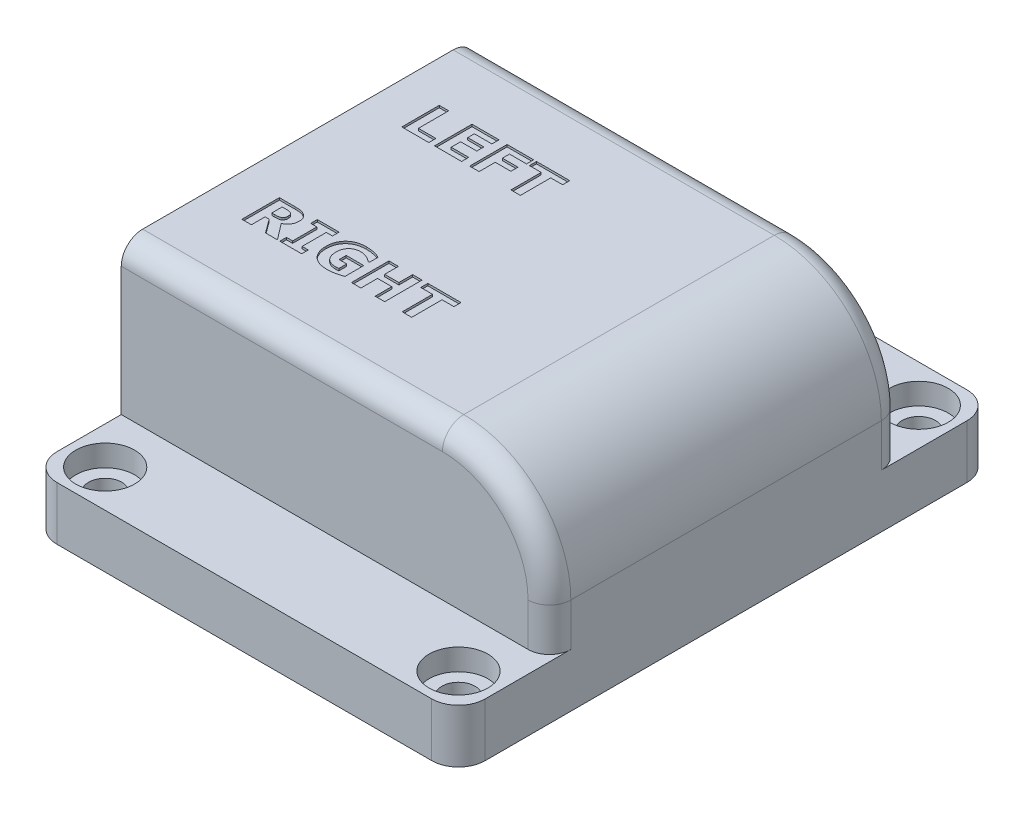
SolidWorks part; units mm, degrees
ref_plane "Front Plane" through (0, 0, 0) normal (0, 0, 1) x (1, 0, 0)
ref_plane "Top Plane" through (0, 0, 0) normal (0, 1, 0) x (1, 0, 0)
ref_plane "Right Plane" through (0, 0, 0) normal (1, 0, 0) x (0, 0, -1)
sketch "Sketch1" plane through (0, 0, 0) normal (0, 1, 0) x (1, 0, 0)
  line L1 (-20, -25) -> (20, -25)
  line L2 (-20, -25) -> (-20, 25)
  line L3 (-20, 25) -> (20, 25)
  line L4 (20, -25) -> (20, 25)
  line L5 (-20, -25) -> (20, 25) construction
  line L6 (-20, 25) -> (20, -25) construction
  point P0 (0, 0)
  dimension "D1" = 50
  dimension "D2" = 40
extrude "Boss-Extrude1" add sketch "Sketch1" along normal blind 5
sketch "Sketch2" plane through (0, 5, 0) normal (0, 1, 0) x (1, 0, 0)
  line L0 (-20, 25) -> (-20, -25) construction
  line L1 (20, -16.5) -> (-20, -16.5)
  line L2 (20, -16.5) -> (20, 16.5)
  line L3 (20, 16.5) -> (-20, 16.5)
  line L4 (-20, -16.5) -> (-20, 16.5)
  line L5 (20, -16.5) -> (-20, 16.5) construction
  line L6 (20, 16.5) -> (-20, -16.5) construction
  point P0 (0, 0)
  dimension "D1" = 33
extrude "Boss-Extrude2" add sketch "Sketch2" along normal blind 14
sketch "Sketch5" plane through (-20, 0, 0) normal (-1, 0, 0) x (0, 0, 1)
  line L0 (0, -1000) -> (0, 49000) construction
  line L1 (-1020.9912, 5) -> (48979.0088, 5) construction
  line L3 (-2, -995) -> (-2, 49005) construction
  line L4 (2, -995) -> (2, 49005) construction
  line L5 (-25, 0) -> (25, 0) construction
  line L6 (-1007.3392, 17.35) -> (48992.6608, 17.35) construction
  line L7 (-14.8, -987.4852) -> (-14.8, 49012.5148) construction
  line L8 (14.8, -989.6407) -> (14.8, 49010.3593) construction
  line L9 (-13.2, -993.3873) -> (-13.2, 49006.6127) construction
  line L10 (-3.6, -993.5926) -> (-3.6, 49006.4074) construction
  line L11 (3.6, -993.3873) -> (3.6, 49006.6127) construction
  line L12 (13.2, -993.6953) -> (13.2, 49006.3047) construction
  line L13 (-1007.9651, 7.5) -> (48992.0349, 7.5) construction
  line L14 (-1008.4622, 7) -> (48991.5378, 7) construction
  line L15 (-2, 5) -> (-3.6, 7)
  line L17 (-13.2, 7) -> (-13.2, 7.5)
  line L18 (-3.6, 7) -> (-3.6, 7.5)
  line L19 (-13.2, 7.5) -> (-14.8, 7.5)
  line L20 (-3.6, 7.5) -> (-2, 7.5)
  line L21 (-14.8, 7.5) -> (-14.8, 17.35)
  line L22 (-14.8, 17.35) -> (-2, 17.35)
  line L23 (-2, 7.5) -> (-2, 17.35)
  line L24 (2, 5) -> (14.8, 5)
  line L25 (2, 5) -> (3.6, 7)
  line L26 (14.8, 5) -> (13.2, 7)
  line L27 (3.6, 7) -> (3.6, 7.5)
  line L28 (13.2, 7) -> (13.2, 7.5)
  line L29 (3.6, 7.5) -> (2, 7.5)
  line L30 (13.2, 7.5) -> (14.8, 7.5)
  line L31 (14.8, 7.5) -> (14.8, 17.35)
  line L32 (2, 7.5) -> (2, 17.35)
  line L33 (2, 17.35) -> (14.8, 17.35)
  line L34 (-2, 5) -> (-13.5, 5)
  line L35 (-13.5, 5) -> (-13.2, 7)
  dimension "D1" = 5
  dimension "D2" = 2
  dimension "D3" = 2
  dimension "D4" = 12.35
  dimension "D5" = 12.8
  dimension "D6" = 12.8
  dimension "D7" = 1.6
  dimension "D8" = 1.6
  dimension "D9" = 1.6
  dimension "D10" = 1.6
  dimension "D11" = 2.5
  dimension "D12" = 2
  dimension "D13" = 3
extrude "Cut-Extrude2" cut sketch "Sketch5" against normal blind 23 contours L35 L34 L15 L18 L20 L23 L22 L21 L19 L17 | L33 L32 L29 L27 L25 L24 L26 L28 L30 L31
sketch "Sketch6" plane through (0, 0, 0) normal (0, -1, 0) x (1, 0, 0)
  line L5 (-1000, 0) -> (49000, 0) construction
  line L6 (-20, -25) -> (-20, 25) construction
  line L7 (3, -15) -> (17, -15)
  line L8 (3, -15) -> (3, 15)
  line L9 (3, 15) -> (17, 15)
  line L10 (17, -15) -> (17, 15)
  line L11 (3, -15) -> (17, 15) construction
  line L12 (3, 15) -> (17, -15) construction
  point P1 (10, 0)
  dimension "D1" = 23
  dimension "D2" = 14
  dimension "D3" = 30
extrude "Cut-Extrude3" cut sketch "Sketch6" against normal blind 17.25
fillet "Fillet1" radius 10 2 edges at (17, 17.25, 0) (20, 19, 0)
sketch "Sketch7" plane through (0, 5, 0) normal (0, 1, 0) x (1, 0, 0)
  line L0 (-17, -989.9572) -> (-17, 49010.0428) construction
  line L1 (-20, 25) -> (-20, 16.5) construction
  line L2 (-1020, 7.75) -> (48980, 7.75) construction
  line L3 (-20, 2) -> (-20, 13.5) construction
  line L4 (-1020, -8.4) -> (48980, -8.4) construction
  line L5 (-20, -2) -> (-20, -14.8) construction
  line L7 (-17, 5.25) -> (-12, 5.25)
  line L8 (-17, 5.25) -> (-17, 10.25)
  line L9 (-17, 10.25) -> (-12, 10.25)
  line L10 (-12, 5.25) -> (-12, 10.25)
  line L11 (-17, 5.25) -> (-12, 10.25) construction
  line L12 (-17, 10.25) -> (-12, 5.25) construction
  line L13 (-17, -10.9) -> (-12, -10.9)
  line L14 (-17, -10.9) -> (-17, -5.9)
  line L15 (-17, -5.9) -> (-12, -5.9)
  line L16 (-12, -10.9) -> (-12, -5.9)
  line L17 (-17, -10.9) -> (-12, -5.9) construction
  line L18 (-17, -5.9) -> (-12, -10.9) construction
  point P9 (-20, 7.75)
  point P10 (-14.5, 7.75)
  point P14 (-20, -8.4)
  point P19 (-14.5, -8.4)
  dimension "D1" = 3
  dimension "D2" = 5
  dimension "D3" = 5
  dimension "D4" = 5
  dimension "D5" = 5
  dimension "D6" = 0
  dimension "D7" = 0
extrude "Cut-Extrude4" cut sketch "Sketch7" against normal blind 0.6
sketch "Sketch8" plane through (0, 5, 0) normal (0, 1, 0) x (1, 0, 0)
  line L0 (-1010.2284, 21.5) -> (48989.7716, 21.5) construction
  line L1 (-1012.553, -21.5) -> (48987.447, -21.5) construction
  line L2 (20, 25) -> (-20, 25) construction
  line L5 (-20, -25) -> (20, -25) construction
  line L6 (-16.5, -977.0857) -> (-16.5, 49022.9143) construction
  line L7 (16.5, -977.4842) -> (16.5, 49022.5158) construction
  line L8 (-20, 25) -> (-20, 16.5) construction
  line L10 (20, 16.5) -> (20, 25) construction
  circle A0 centre (-16.5, 21.5) radius 1.55
  circle A1 centre (16.5, 21.5) radius 1.55
  circle A2 centre (16.5, -21.5) radius 1.55
  circle A3 centre (-16.5, -21.5) radius 1.55
  dimension "D6" = 3.1
  dimension "D8" = 3.1
  dimension "D10" = 3.1
  dimension "D12" = 3.1
  dimension "D1" = 3.5
  dimension "D2" = 3.5
  dimension "D3" = 3.5
  dimension "D4" = 3.5
  dimension "D5" = 0
  dimension "D7" = 0
  dimension "D9" = 0
  dimension "D11" = 0
extrude "Cut-Extrude5" cut sketch "Sketch8" against normal through all both and the other way through all
sketch "Sketch9" plane through (0, 5, 0) normal (0, 1, 0) x (1, 0, 0)
  circle A0 centre (-16.5, 21.5) radius 2.75
  circle A1 centre (16.5, 21.5) radius 2.75
  circle A2 centre (16.5, -21.5) radius 2.75
  circle A3 centre (-16.5, -21.5) radius 2.75
  dimension "D1" = 5.5
  dimension "D2" = 5.5
  dimension "D3" = 5.5
  dimension "D4" = 5.5
extrude "Cut-Extrude6" cut sketch "Sketch9" against normal blind 2
fillet "Fillet2" radius 2.5 4 edges at (20, 2.5, -25) (20, 2.5, 25) (-20, 2.5, 25) (-20, 2.5, -25)
fillet "Fillet3" radius 2 6 edges at (20, 7, -16.5) (17.0711, 16.0711, -16.5) (20, 7, 16.5) (17.0711, 16.0711, 16.5) (-5, 19, -16.5) (-5, 19, 16.5)
sketch "Sketch11" plane through (0, 19, 0) normal (0, 1, 0) x (1, 0, 0)
  line L0 (-1000, 0) -> (49000, 0) construction
  line L1 (-1004.5347, 7.5) -> (48995.4653, 7.5) construction
  line L2 (-996.7324, -7.5) -> (49003.2676, -7.5) construction
  text T0 "LEFT" font "Verdana" height 3.5
  text T1 "RIGHT" font "Verdana" height 3.5
  point P6 (0, 0)
  point P7 (-16.6049, -9.2694)
  point P8 (-16.6049, -9.3361)
  point P9 (-16.6049, -8.9359)
  point P10 (-16.6049, -9.3361)
  point P12 (-16.6049, -9.0693)
  point P13 (0, 0)
  point P14 (-16.6049, 2.2269)
  point P15 (-3.5787, 2.8302)
  point P16 (0, 0)
  point P18 (-16.6049, 5.8684)
  dimension "D1" = 7.5
  dimension "D2" = 7.5
extrude "Cut-Extrude8" cut sketch "Sketch11" against normal blind 0.2
